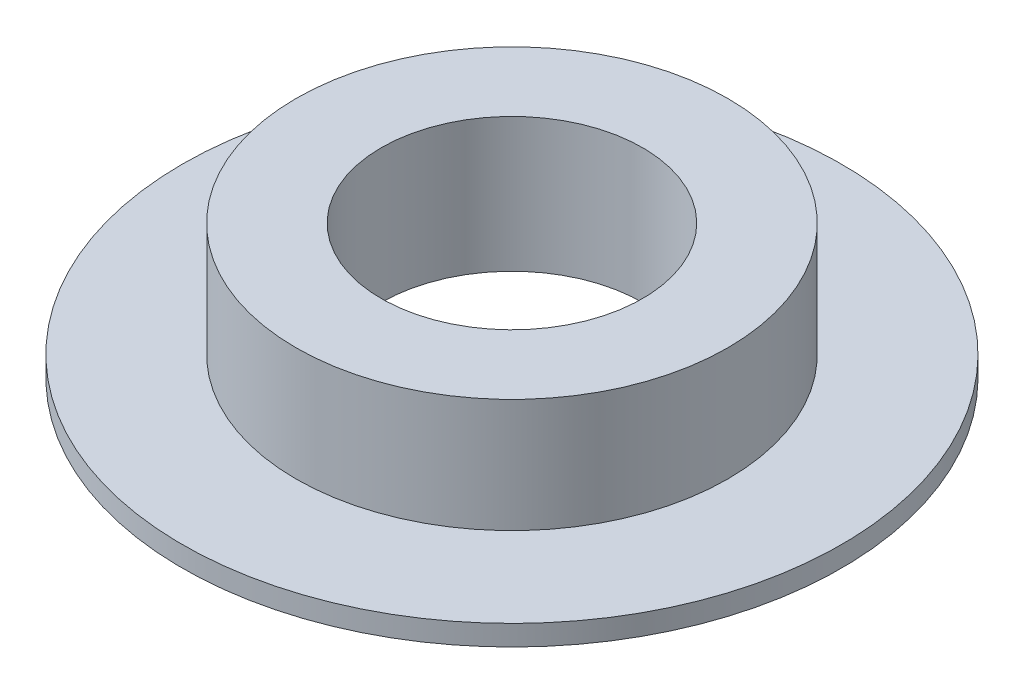
SolidWorks part; units mm, degrees
ref_plane "Alzado" through (0, 0, 0) normal (0, 0, 1) x (1, 0, 0)
ref_plane "Planta" through (0, 0, 0) normal (0, 1, 0) x (1, 0, 0)
ref_plane "Vista lateral" through (0, 0, 0) normal (1, 0, 0) x (0, 0, -1)
sketch "Croquis1" plane through (0, 0, 0) normal (0, 0, 1) x (1, 0, 0)
  line L0 (-37.0216, 13.9729) -> (-37.0216, -36.0271) construction
  line L1 (-37.0216, -11.0271) -> (-48.5216, -11.0271) construction
  line L2 (-48.5216, 8.9729) -> (-48.5216, -2.8271)
  line L3 (-37.0216, 8.9729) -> (-56.0216, 8.9729) construction
  line L4 (-48.5216, 8.9729) -> (-56.0216, 8.9729)
  line L5 (-56.0216, 8.9729) -> (-56.0216, -1.0271)
  line L6 (-56.0216, -1.0271) -> (-66.0216, -1.0271)
  line L7 (-66.0216, -1.0271) -> (-66.0216, -2.8271)
  line L8 (-66.0216, -2.8271) -> (-48.5216, -2.8271)
  dimension "D1" = 19
  dimension "D2" = 11.5
  dimension "D3" = 1.8
  dimension "D4" = 10
  dimension "D5" = 11.5
  dimension "D6" = 10
revolve "Revolución1" add sketch "Croquis1" angle 360 about L0
